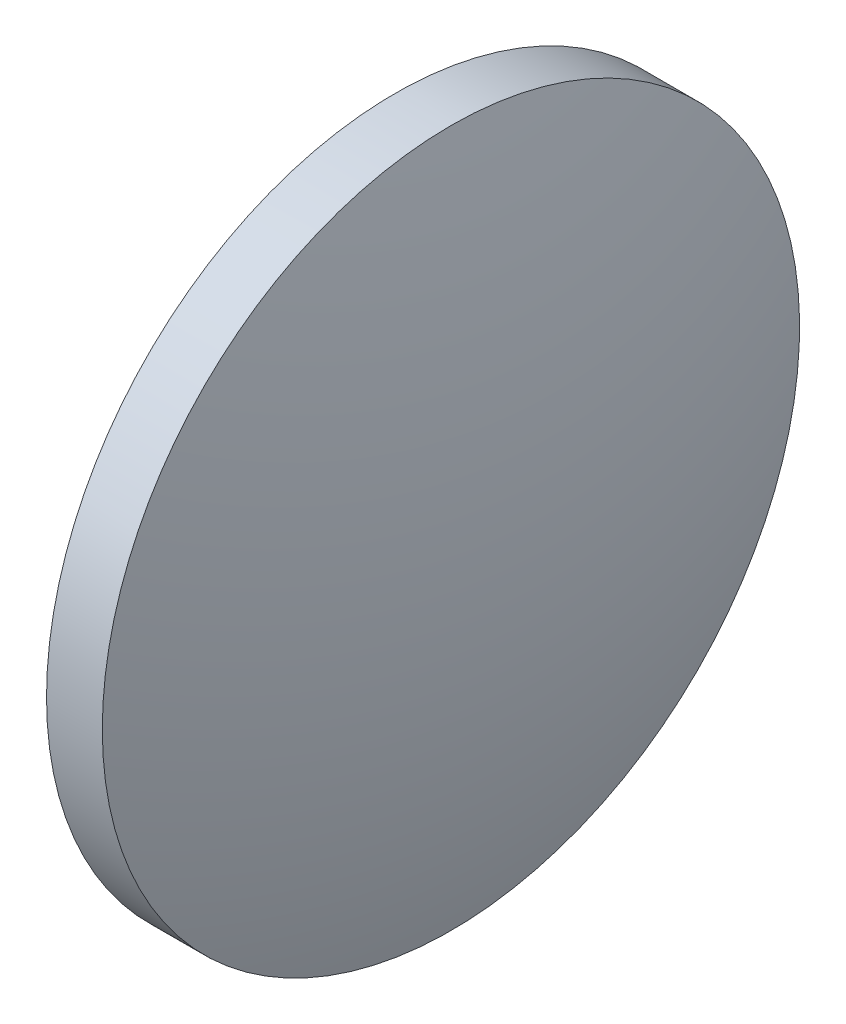
SolidWorks part; units mm, degrees
ref_plane "前视基准面" through (0, 0, 0) normal (0, 0, 1) x (1, 0, 0)
ref_plane "上视基准面" through (0, 0, 0) normal (0, 1, 0) x (1, 0, 0)
ref_plane "右视基准面" through (0, 0, 0) normal (1, 0, 0) x (0, 0, -1)
sketch "草图1" plane through (0, 0, 0) normal (0, 0, 1) x (1, 0, 0)
  line L0 (724.0748, 258.8552) -> (737.5205, 258.8552) construction
  line L1 (728.8168, 258.8552) -> (728.8168, 271.3552)
  line L2 (732.7568, 258.8552) -> (728.8168, 258.8552)
  line L5 (728.8168, 271.3552) -> (730.8168, 271.3552)
  arc A0 (732.7568, 258.8552) -> (730.8168, 271.3552) centre (691.5162, 258.8552) ccw
revolve "旋转1" add sketch "草图1" angle 360 about L0
